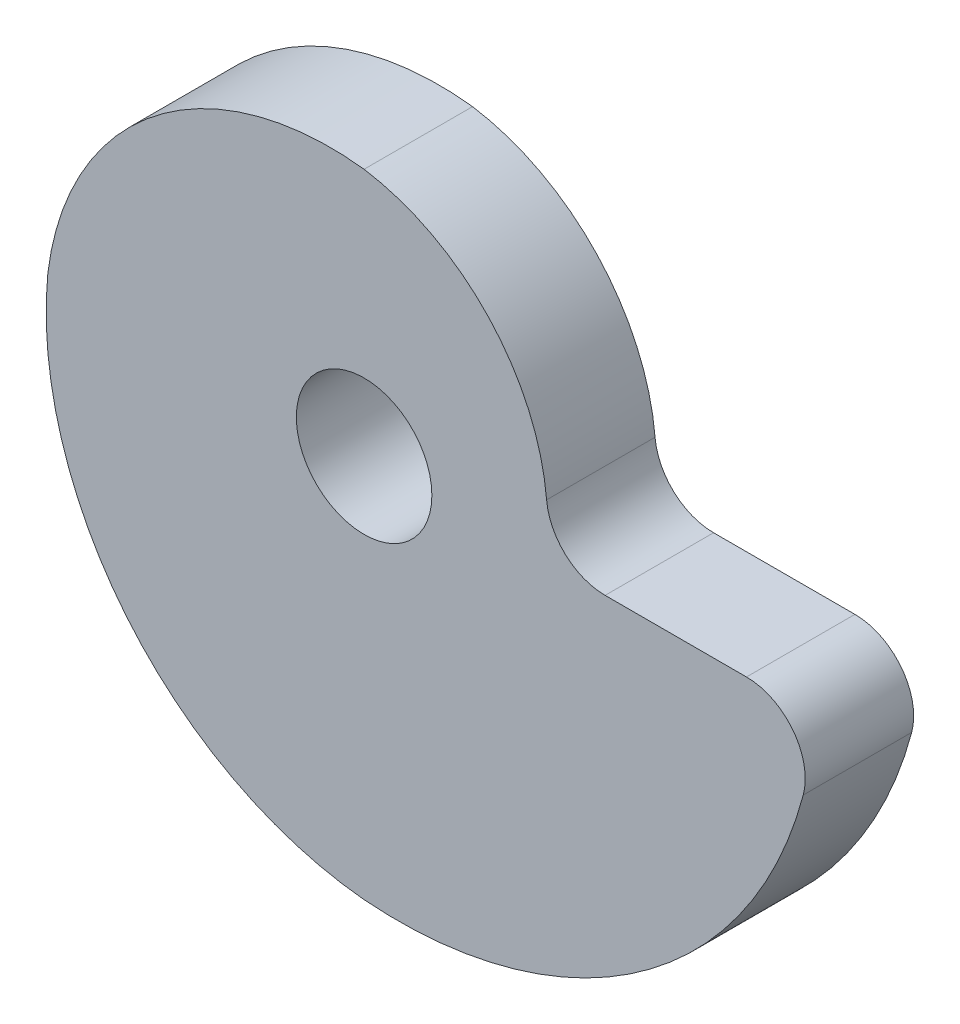
SolidWorks part; units mm, degrees
ref_plane "Front Plane" through (0, 0, 0) normal (0, 0, 1) x (1, 0, 0)
ref_plane "Top Plane" through (0, 0, 0) normal (0, 1, 0) x (1, 0, 0)
ref_plane "Right Plane" through (0, 0, 0) normal (1, 0, 0) x (0, 0, -1)
sketch "Sketch1" plane through (0, 0, 0) normal (0, 0, 1) x (1, 0, 0)
  line L0 (8, 0) -> (20, 0)
  circle A0 centre (0, 0) radius 3
  arc A6 (8, 0) -> (0, 11) centre (-1.5, 1.5) ccw
  arc A7 (0, 11) -> (-14, 0) centre (-1.5, -1.5) ccw
  arc A8 (-14, 0) -> (0, -17) centre (1.5, -1.5) ccw
  arc A9 (0, -17) -> (20, 0) centre (1.5, 1.5) ccw
  point P3 (-14, 0)
  point P4 (0, -17)
  point P7 (0, 11)
  dimension "D1" = 0
  dimension "D2" = 11
  dimension "D3" = 6
  dimension "D4" = 14
  dimension "D5" = 8
  dimension "D6" = 17
  dimension "D9" = 18.5607
  dimension "D10" = 9.6177
  dimension "D11" = 12.5897
  dimension "D12" = 15.5724
  dimension "D7" = 0
  dimension "D8" = 0
  dimension "D13" = 12
extrude "Boss-Extrude1" add sketch "Sketch1" along normal mid plane 4.8
fillet "Fillet1" radius 2.6 2 edges at (20, 0, 0) (8, 0, 0)
sketch "Sketch3" plane through (0, 0, 0) normal (0, 0, 1) x (1, 0, 0)
  line L1 (15.091, 6.2633) -> (6.8553, 6.2633)
  line L2 (16.9251, 0) -> (10.6681, 0)
  line L4 (19.5251, -2.6) -> (31.9249, -2.6) construction
  line L5 (17.9623, 6.2633) -> (19.5251, -2.6) construction
  arc A3 (19.4379, -3.2679) -> (16.9251, 0) centre (16.9251, -2.6) ccw construction
  arc A4 (8.0786, 2.3659) -> (0, 11) centre (-1.5, 1.5) ccw construction
  arc A5 (15.091, 6.2633) -> (18.9756, 3.2172) centre (15.091, 2.2633) cw
  arc A7 (8.0786, 2.3659) -> (0, 11) centre (-1.5, 1.5) ccw
  arc A8 (6.8553, 6.2633) -> (0, 11) centre (-1.5, 1.5) ccw
  arc A9 (19.4379, -3.2679) -> (16.9251, 0) centre (16.9251, -2.6) ccw
  arc A10 (0, 11) -> (-14, 0) centre (-1.5, -1.5) ccw
  arc A11 (0, 11) -> (-14, 0) centre (-1.5, -1.5) ccw
  arc A12 (0, -17) -> (19.4379, -3.2679) centre (1.5, 1.5) ccw
  arc A13 (19.4379, -3.2679) -> (16.9251, 0) centre (16.9251, -2.6) ccw
  arc A14 (8.0786, 2.3659) -> (10.6681, 0) centre (10.6681, 2.6) ccw
  arc A15 (8.0786, 2.3659) -> (0, 11) centre (-1.5, 1.5) ccw
  arc A16 (0, 11) -> (-14, 0) centre (-1.5, -1.5) ccw
  arc A17 (-14, 0) -> (0, -17) centre (1.5, -1.5) ccw
  arc A18 (0, -17) -> (19.4379, -3.2679) centre (1.5, 1.5) ccw
  arc A23 (-14, 0) -> (0, -17) centre (1.5, -1.5) ccw
  arc A24 (19.4379, -3.2679) -> (19.5251, -2.6) centre (16.9251, -2.6) ccw
  arc A25 (19.5251, -2.6) -> (18.9756, 3.2172) centre (-0.4474, -1.5523) ccw
  point P13 (17.9623, 6.2633)
  dimension "D2" = 0
  dimension "D7" = 100
  dimension "D6" = 40
  dimension "D8" = 4
  dimension "D4" = 9
  dimension "D1" = 0
  dimension "D3" = 0
  dimension "D5" = 0
